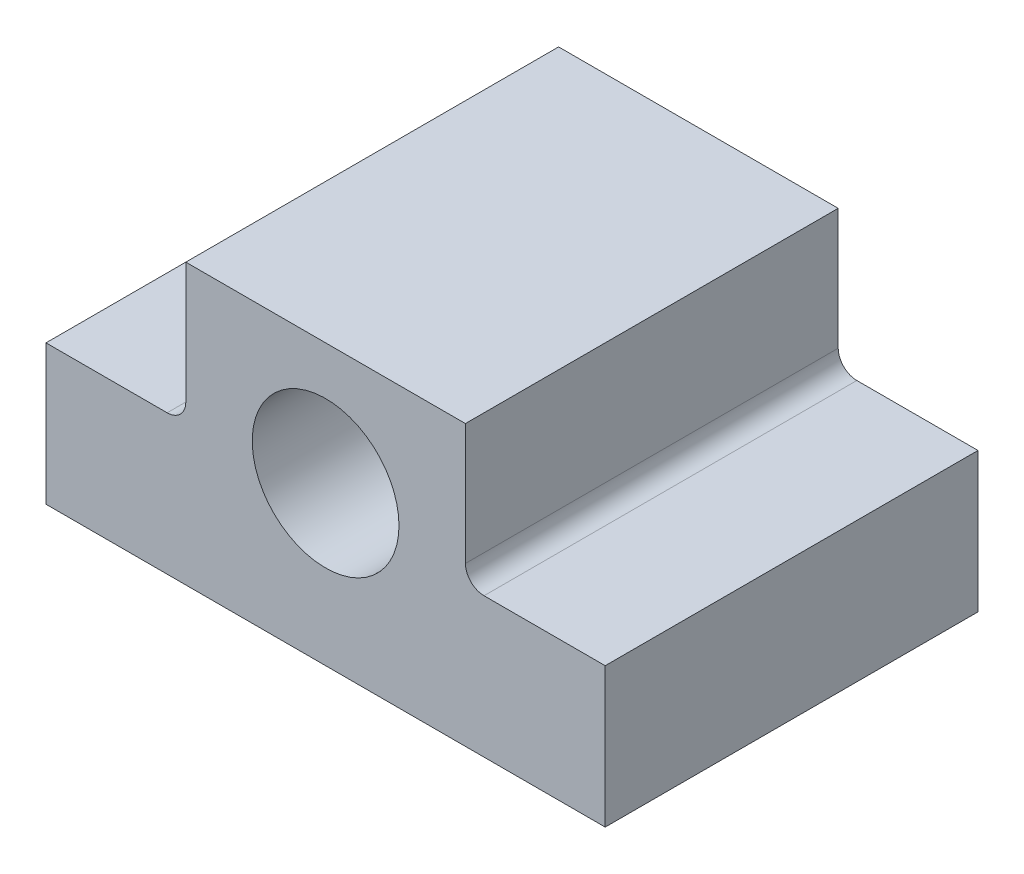
SolidWorks part; units mm, degrees
ref_plane "Front Plane" through (0, 0, 0) normal (0, 0, 1) x (1, 0, 0)
ref_plane "Top Plane" through (0, 0, 0) normal (0, 1, 0) x (1, 0, 0)
ref_plane "Right Plane" through (0, 0, 0) normal (1, 0, 0) x (0, 0, -1)
sketch "Sketch1" plane through (0, 0, 0) normal (0, 0, 1) x (1, 0, 0)
  line L0 (-19.05, 0) -> (19.05, 0)
  line L1 (19.05, 0) -> (19.05, 9.525)
  line L2 (19.05, 9.525) -> (9.525, 9.525)
  line L3 (9.525, 9.525) -> (9.525, 19.05)
  line L4 (9.525, 19.05) -> (-9.525, 19.05)
  line L5 (-9.525, 19.05) -> (-9.525, 9.525)
  line L6 (-9.525, 9.525) -> (-19.05, 9.525)
  line L7 (-19.05, 9.525) -> (-19.05, 0)
  circle A0 centre (0, 10.7645) radius 5
  point P3 (0, 19.05)
  point P12 (-9.525, 14.2875)
  dimension "D4" = 10
  dimension "D1" = 38.1
  dimension "D2" = 19.05
  dimension "D3" = 19.05
extrude "Boss-Extrude1" add sketch "Sketch1" along normal mid plane 25.4
fillet "Fillet1" radius 1.27 2 edges at (9.525, 9.525, 0) (-9.525, 9.525, 0)
